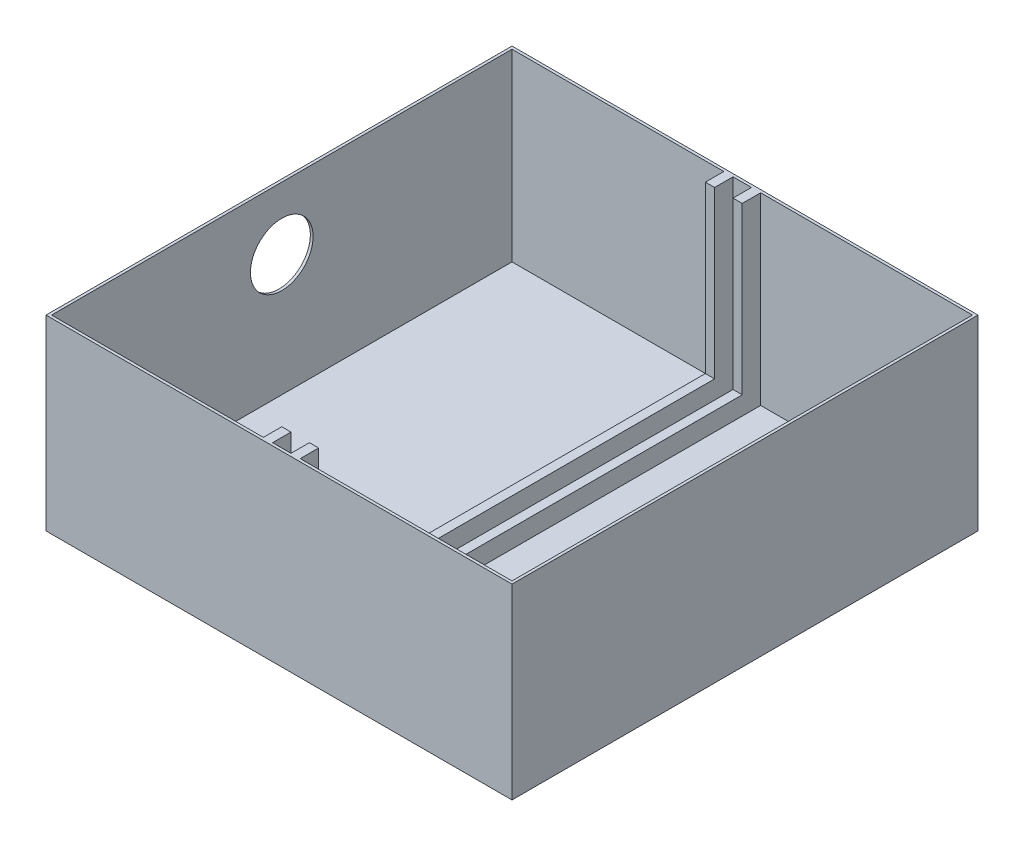
SolidWorks part; units mm, degrees
ref_plane "Front Plane" through (0, 0, 0) normal (0, 0, 1) x (1, 0, 0)
ref_plane "Top Plane" through (0, 0, 0) normal (0, 1, 0) x (1, 0, 0)
ref_plane "Right Plane" through (0, 0, 0) normal (1, 0, 0) x (0, 0, -1)
sketch "Sketch1" plane through (0, 0, 0) normal (0, 1, 0) x (1, 0, 0)
  line L1 (-126.5, 126.5) -> (126.5, 126.5)
  line L2 (-126.5, 126.5) -> (-126.5, -126.5)
  line L3 (-126.5, -126.5) -> (126.5, -126.5)
  line L4 (126.5, 126.5) -> (126.5, -126.5)
  line L5 (-126.5, 126.5) -> (126.5, -126.5) construction
  line L6 (-126.5, -126.5) -> (126.5, 126.5) construction
  point P0 (0, 0)
  dimension "D2" = 253
extrude "Boss-Extrude1" add sketch "Sketch1" along normal blind 101.5
shell "Shell2" thickness 1.5
sketch "Sketch2" plane through (0, 1.5, 0) normal (0, 1, 0) x (1, 0, 0)
  line L0 (0, -126.5) -> (0, 126.5) construction
  line L1 (-126.5, -126.5) -> (126.5, -126.5) construction
  line L2 (126.5, 126.5) -> (-126.5, 126.5) construction
  line L3 (-126.5, 0) -> (126.5, 0) construction
  line L4 (-126.5, 126.5) -> (-126.5, -126.5) construction
  line L5 (126.5, -126.5) -> (126.5, 126.5) construction
  line L6 (-10, 125) -> (-10, 115)
  line L7 (125, 125) -> (-125, 125) construction
  line L8 (-10, 115) -> (-5, 115)
  line L9 (-5, 115) -> (-5, 125)
  line L10 (5, 115) -> (5, 125)
  line L11 (10, 125) -> (10, 115)
  line L12 (10, 115) -> (5, 115)
  line L13 (10, -125) -> (10, -115)
  line L14 (10, -115) -> (5, -115)
  line L15 (5, -115) -> (5, -125)
  line L16 (-5, -115) -> (-5, -125)
  line L17 (-10, -115) -> (-5, -115)
  line L18 (-10, -125) -> (-10, -115)
  line L19 (-10, 125) -> (-5, 125)
  line L20 (10, 125) -> (5, 125)
  line L21 (10, -125) -> (5, -125)
  line L22 (-10, -125) -> (-5, -125)
  line L23 (-10, -115) -> (-10, 115)
  line L24 (-5, 115) -> (-5, -115)
  line L25 (5, 115) -> (5, -115)
  line L26 (10, -115) -> (10, 115)
  dimension "D1" = 5
  dimension "D2" = 10
  dimension "D3" = 5
extrude "Boss-Extrude3" add sketch "Sketch2" along normal blind 10 contours L24 L8 L23 L17 | L14 L26 L12 L25 | L9 L19 L6
sketch "Sketch3" plane through (0, 1.5, 0) normal (0, 1, 0) x (1, 0, 0)
  line L0 (-10, 115) -> (-10, 125)
  line L1 (125, 125) -> (-125, 125) construction
  line L2 (-10, 125) -> (-5, 125)
  line L3 (-5, 125) -> (-5, 115)
  line L4 (-5, 115) -> (-10, 115)
  line L5 (0, 0) -> (0, 125) construction
  line L6 (125, 125) -> (-125, 125) construction
  line L7 (0, 0) -> (10, 0) construction
  line L8 (10, -115) -> (10, 115) construction
  line L9 (10, 115) -> (10, 125)
  line L10 (10, 125) -> (5, 125)
  line L11 (5, 115) -> (10, 115)
  line L12 (5, 125) -> (5, 115)
  line L13 (5, -125) -> (5, -115)
  line L14 (5, -115) -> (10, -115)
  line L15 (10, -125) -> (5, -125)
  line L16 (10, -115) -> (10, -125)
  line L17 (-5, -115) -> (-10, -115)
  line L18 (-5, -125) -> (-5, -115)
  line L19 (-10, -125) -> (-5, -125)
  line L20 (-10, -115) -> (-10, -125)
extrude "Boss-Extrude4" add sketch "Sketch3" along normal up to surface (100 mm away) up to face at (0, 101.5, 0)
sketch "Sketch4" plane through (-126.5, 0, 0) normal (-1, 0, 0) x (0, 0, 1)
  line L0 (-126.5, 101.5) -> (126.5, 101.5) construction
  circle A0 centre (0, 67.5) radius 17
  dimension "D1" = 34
  dimension "D2" = 34
extrude "Cut-Extrude1" cut sketch "Sketch4" against normal up to surface (1.5 mm away) up to face at (-125, 51.5, 0)
